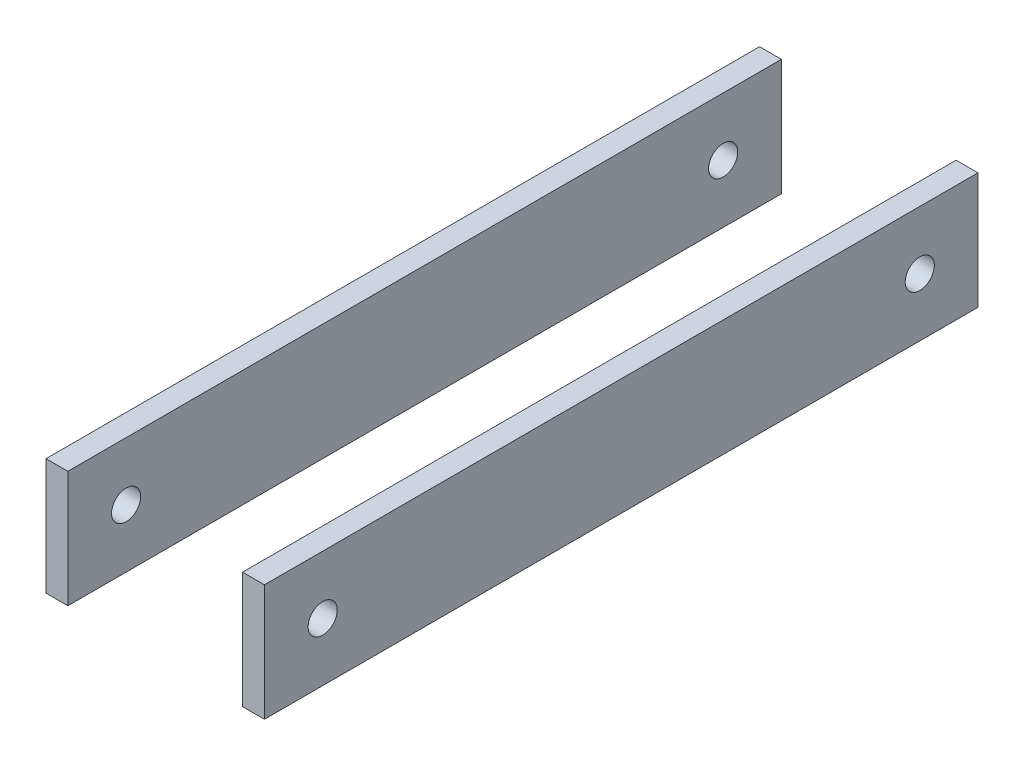
SolidWorks part; units mm, degrees
ref_plane "Front Plane" through (0, 0, 0) normal (0, 0, 1) x (1, 0, 0)
ref_plane "Top Plane" through (0, 0, 0) normal (0, 1, 0) x (1, 0, 0)
ref_plane "Right Plane" through (0, 0, 0) normal (1, 0, 0) x (0, 0, -1)
sketch "Sketch1" plane through (0, 0, 0) normal (1, 0, 0) x (0, 0, -1)
  line L1 (-152.4, 25.4) -> (158.75, 25.4)
  line L2 (-152.4, 25.4) -> (-152.4, -25.4)
  line L3 (-152.4, -25.4) -> (158.75, -25.4)
  line L4 (158.75, 25.4) -> (158.75, -25.4)
  circle A0 centre (-127, 0) radius 6.35
  circle A1 centre (133.35, 0) radius 6.35
  dimension "D5" = 12.7
  dimension "D6" = 12.7
  dimension "D7" = 25.4
  dimension "D8" = 25.4
  dimension "D1" = 311.15
  dimension "D2" = 50.8
  dimension "D3" = 152.4
  dimension "D4" = 25.4
extrude "Boss-Extrude1" add sketch "Sketch1" along normal mid plane 95.25
sketch "Sketch2" plane through (0, 0, 152.4) normal (0, 0, 1) x (1, 0, 0)
  line L0 (47.625, 25.4) -> (-47.625, 25.4) construction
  line L1 (-38.1, 25.4) -> (38.1, 25.4)
  line L2 (-38.1, 25.4) -> (-38.1, -25.4)
  line L3 (-38.1, -25.4) -> (38.1, -25.4)
  line L4 (38.1, 25.4) -> (38.1, -25.4)
  line L5 (47.625, -25.4) -> (-47.625, -25.4) construction
  dimension "D1" = 76.2
  dimension "D2" = 38.1
extrude "Cut-Extrude1" cut sketch "Sketch2" against normal blind 311.15
